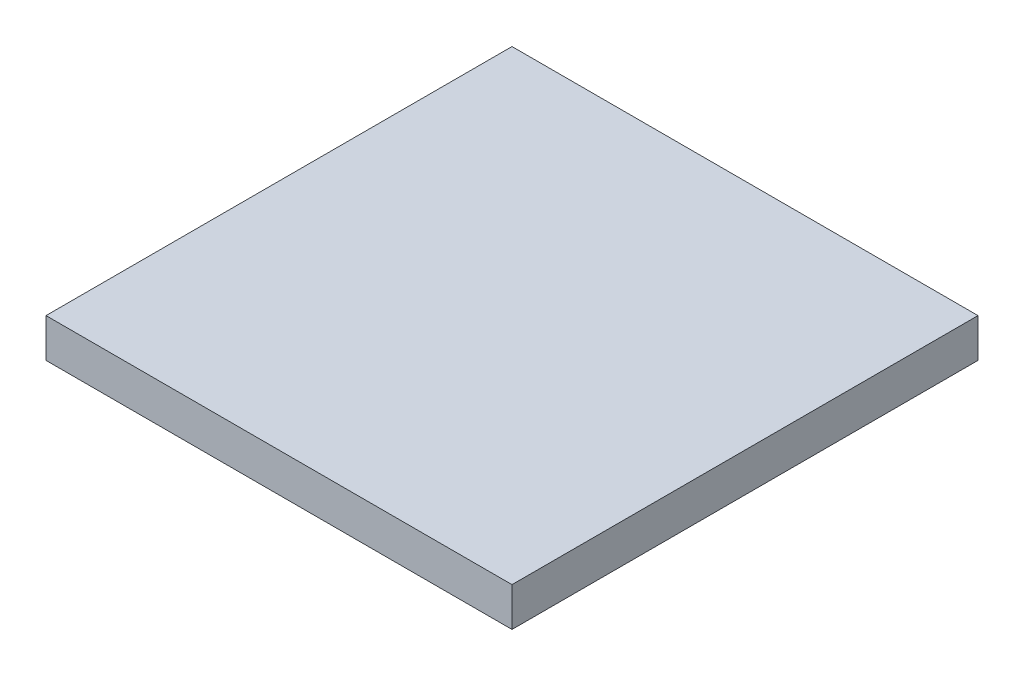
SolidWorks part; units mm, degrees
ref_plane "Ön Düzlem" through (0, 0, 0) normal (0, 0, 1) x (1, 0, 0)
ref_plane "Üst Düzlem" through (0, 0, 0) normal (0, 1, 0) x (1, 0, 0)
ref_plane "Sağ Düzlem" through (0, 0, 0) normal (1, 0, 0) x (0, 0, -1)
sketch "Çizim1" plane through (0, 0, 0) normal (0, 1, 0) x (1, 0, 0)
  line L1 (-11.94, 5.46) -> (11.94, 5.46)
  line L2 (-11.94, 5.46) -> (-11.94, -5.46)
  line L3 (-11.94, -5.46) -> (11.94, -5.46)
  line L4 (11.94, 5.46) -> (11.94, -5.46)
  line L5 (-11.94, 5.46) -> (11.94, -5.46) construction
  line L6 (-11.94, -5.46) -> (11.94, 5.46) construction
  point P0 (0, 0)
  dimension "D1" = 10.92
  dimension "D2" = 23.88
extrude "Yükseklik-Ekstrüzyon5" add sketch "Çizim1" along normal blind 10
sketch "Çizim4" plane through (0, 10, 0) normal (0, 1, 0) x (1, 0, 0)
  line L1 (-30, 30) -> (30, 30)
  line L2 (-30, 30) -> (-30, -30)
  line L3 (-30, -30) -> (30, -30)
  line L4 (30, 30) -> (30, -30)
  line L5 (-30, 30) -> (30, -30) construction
  line L6 (-30, -30) -> (30, 30) construction
  point P0 (0, 0)
  dimension "D1" = 60
  dimension "D2" = 60
extrude "Yükseklik-Ekstrüzyon6" add sketch "Çizim4" along normal blind 5
sketch "Çizim5" plane through (0, 0, 5.46) normal (0, 0, 1) x (1, 0, 0)
  line L0 (11.94, 0) -> (11.94, 4.5) construction
  line L1 (11.94, 10) -> (11.94, 0) construction
  line L2 (11.94, 4.5) -> (11.94, 9) construction
  line L3 (11.94, 2.25) -> (9.64, 2.25) construction
  line L4 (11.94, 6.75) -> (9.64, 6.75) construction
  line L5 (0, 13.4566) -> (0, -2.888) construction
  line L6 (-11.94, 6.75) -> (-9.64, 6.75) construction
  line L7 (-11.94, 2.25) -> (-9.64, 2.25) construction
  line L8 (-11.94, 0) -> (-11.94, 4.5) construction
  circle A0 centre (9.64, 2.25) radius 1
  circle A1 centre (9.64, 6.75) radius 1
  circle A2 centre (-9.64, 6.75) radius 1
  circle A3 centre (-9.64, 2.25) radius 1
  dimension "D5" = 2
  dimension "D6" = 2
  dimension "D1" = 4.5
  dimension "D2" = 4.5
  dimension "D3" = 2.3
  dimension "D4" = 2.3
extrude "Kes-Ekstrüzyon1" cut sketch "Çizim5" against normal blind 3
sketch "Çizim6" plane through (0, 0, -5.46) normal (0, 0, -1) x (-1, 0, 0)
  line L0 (11.94, 0) -> (11.94, 4.5) construction
  line L1 (11.94, 10) -> (11.94, 0) construction
  line L2 (11.94, 4.5) -> (11.94, 9) construction
  line L3 (11.94, 2.25) -> (9.64, 2.25) construction
  line L4 (11.94, 6.75) -> (9.64, 6.75) construction
  line L5 (0, 13.9572) -> (0, -1.8271) construction
  line L6 (-11.94, 6.75) -> (-9.64, 6.75) construction
  line L7 (-11.94, 2.25) -> (-9.64, 2.25) construction
  line L8 (-11.94, 4.5) -> (-11.94, 9) construction
  line L9 (-11.94, 0) -> (-11.94, 4.5) construction
  circle A0 centre (9.64, 2.25) radius 1
  circle A1 centre (9.64, 6.75) radius 1
  circle A2 centre (-9.64, 6.75) radius 1
  circle A3 centre (-9.64, 2.25) radius 1
  dimension "D5" = 2
  dimension "D6" = 2
  dimension "D1" = 4.5
  dimension "D2" = 4.5
  dimension "D3" = 2.3
  dimension "D4" = 2.3
extrude "Kes-Ekstrüzyon2" cut sketch "Çizim6" against normal blind 3
scale "Ölçek1" scale about centroid uniform scaling yes scale factor 0.5
